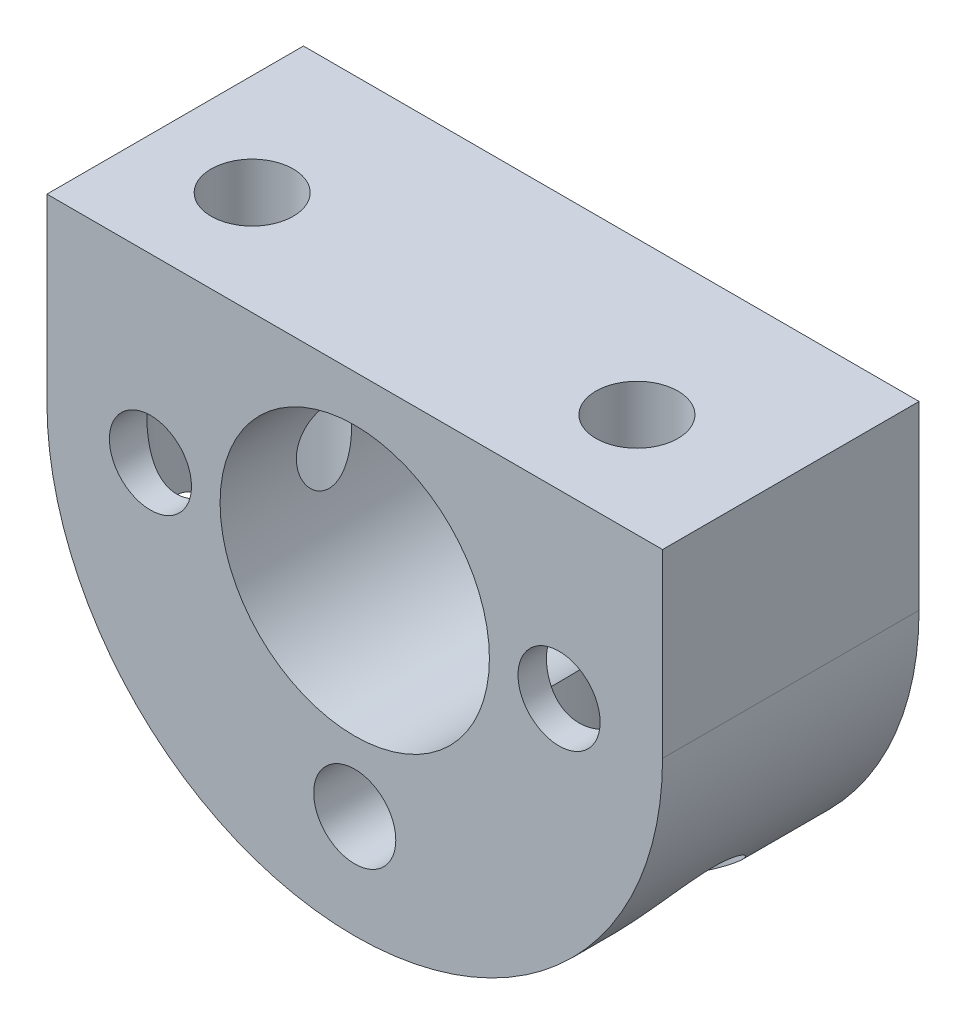
SolidWorks part; units mm, degrees
material "Thornel Mat VMA"
ref_plane "Plano frontal" through (0, 0, 0) normal (0, 0, 1) x (1, 0, 0)
ref_plane "Plano superior" through (0, 0, 0) normal (0, 1, 0) x (1, 0, 0)
ref_plane "Plano direito" through (0, 0, 0) normal (1, 0, 0) x (0, 0, -1)
sketch "Esboço1" plane through (0, 0, 0) normal (0, 0, 1) x (1, 0, 0)
  line L0 (115.6466, -302.7659) -> (115.6466, -295.7159)
  line L1 (92.6466, -295.7159) -> (114.6466, -295.7159) construction
  line L2 (91.6466, -302.7659) -> (91.6466, -295.7159)
  line L3 (92.6466, -302.7659) -> (92.6466, -295.7159) construction
  line L4 (91.6466, -295.7159) -> (115.6466, -295.7159)
  line L5 (114.6466, -302.7659) -> (114.6466, -295.7159) construction
  line L6 (91.6466, -294.7159) -> (115.6466, -294.7159) construction
  line L7 (91.6466, -302.7659) -> (91.6466, -294.7159) construction
  line L8 (115.6466, -302.7659) -> (115.6466, -294.7159) construction
  circle A0 centre (103.6466, -302.7659) radius 7.9647 construction
  arc A1 (92.6466, -302.7659) -> (114.6466, -302.7659) centre (103.6466, -302.7659) ccw construction
  arc A2 (91.6466, -302.7659) -> (115.6466, -302.7659) centre (103.6466, -302.7659) ccw
  dimension "D1" = 11
  dimension "D2" = 1
extrude "Ressalto-extrusão1" add sketch "Esboço1" along normal blind 10
sketch "Sketch4" [suppressed] plane through (0, 0, 9) normal (0, 0, 1) x (1, 0, 0)
  line L1 (92.6466, -295.7159) -> (114.6466, -295.7159)
  line L2 (92.6466, -295.7159) -> (92.6466, -299.8338)
  line L3 (92.6466, -299.8338) -> (114.6466, -299.8338)
  line L4 (114.6466, -295.7159) -> (114.6466, -299.8338)
sketch "Esboço2" plane through (0, 0, 10) normal (0, 0, 1) x (1, 0, 0)
  circle A0 centre (103.6466, -302.7659) radius 5.25
  dimension "10.5" = 10.5
extrude "Corte-extrusão1" cut sketch "Esboço2" against normal blind 31.8 and the other way blind 16
ref_plane "Plane1" through (0, -314.7159, 0) normal (0, 1, 0) x (1, 0, 0)
sketch "Sketch8" plane through (0, 0, 10) normal (0, 0, 1) x (1, 0, 0)
  line L3 (115.6466, -295.7159) -> (91.6466, -295.7159)
  line L4 (115.6466, -295.7159) -> (91.6466, -295.7159)
  line L5 (115.6466, -302.7659) -> (115.6466, -295.7159)
  line L6 (115.6466, -302.7659) -> (115.6466, -295.7159)
  line L7 (91.6466, -295.7159) -> (91.6466, -302.7659)
  line L8 (91.6466, -295.7159) -> (91.6466, -302.7659)
  arc A1 (91.6466, -302.7659) -> (115.6466, -302.7659) centre (103.6466, -302.7659) ccw
  arc A2 (91.6466, -302.7659) -> (115.6466, -302.7659) centre (103.6466, -302.7659) ccw
  dimension "D1" = 0
extrude "Boss-Extrude2" [suppressed] add sketch "Sketch8" along normal blind 5
hole_wizard "CBORE for M5 Hex Head Bolt1" positions "Sketch6" profile "Sketch5" counterbore size "M5" standard "DIN" end condition through all
sketch "Sketch6" plane through (0, -314.7159, 0) normal (0, -1, 0) x (-1, 0, 0)
  point P0 (-95.5966, -5.9493)
  point P3 (-110.5966, -5.9493)
sketch "Sketch5" plane through (95.5966, -314.7159, 5.9493) normal (1, 0, 0) x (0, 0, -1)
  line L0 (0, 0) -> (0, 19)
  line L1 (0, 19) -> (1.6, 19)
  line L3 (1.6, 19) -> (1.6, 16.5)
  line L4 (1.6, 16.5) -> (3, 16.5)
  line L5 (3, 16.5) -> (3, 0)
  line L7 (3, 0) -> (0, 0)
  line L11 (0, -6.35) -> (0, 107.95) construction
  dimension "Thru Hole Dia." = 3.2
  dimension "Thru Hole Depth" = 19
  dimension "C'Bore Dia." = 6
  dimension "C'Bore Depth" = 16.5
hole_wizard "M3 Clearance Hole5" positions "Sketch10" profile "Sketch9" hole size "M3" standard "ISO" end condition through all
sketch "Sketch10" plane through (0, 0, 10) normal (0, 0, 1) x (1, 0, 0)
  point P0 (95.6819, -302.7659)
  point P2 (103.6466, -310.7307)
  point P4 (111.6113, -302.7659)
sketch "Sketch9" plane through (95.6819, -302.7659, 10) normal (1, 0, 0) x (0, -1, 0)
  line L0 (0, 0) -> (0, 10)
  line L1 (0, 10) -> (1.6, 10)
  line L2 (1.6, 10) -> (1.6, 0)
  line L5 (1.6, 0) -> (0, 0)
  line L11 (0, -6.35) -> (0, 107.95) construction
  dimension "Thru Hole Dia." = 3.2
  dimension "Thru Hole Depth" = 10
